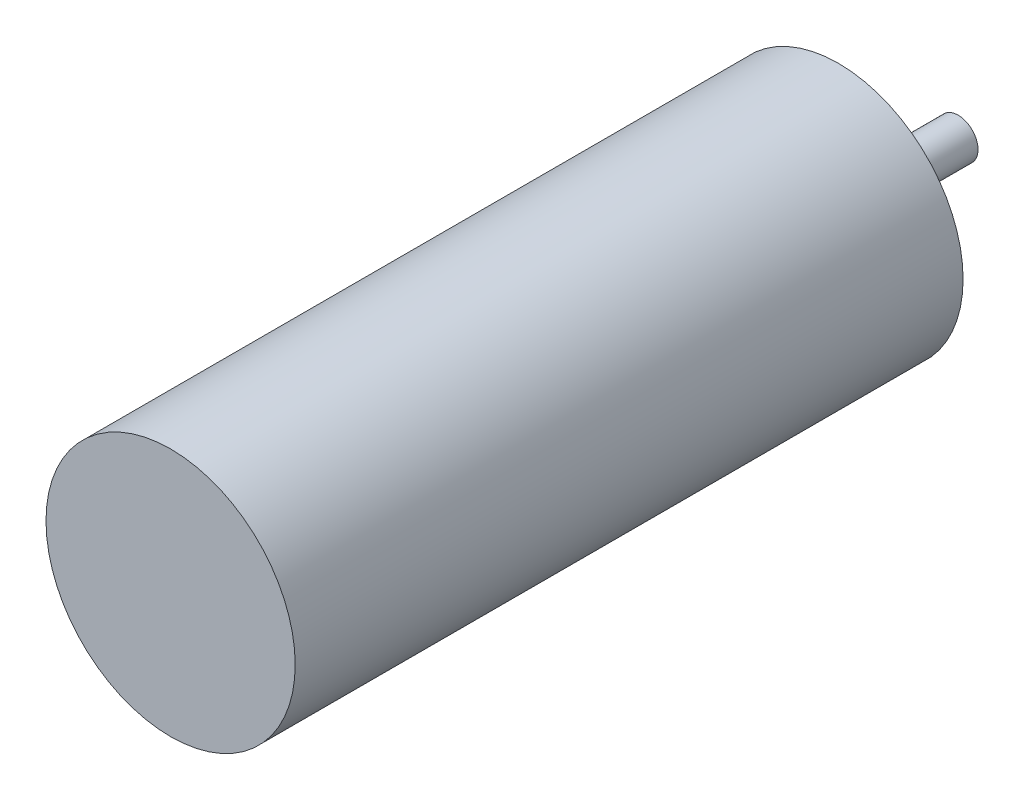
SolidWorks part; units mm, degrees
ref_plane "Front Plane" through (0, 0, 0) normal (0, 0, 1) x (1, 0, 0)
ref_plane "Top Plane" through (0, 0, 0) normal (0, 1, 0) x (1, 0, 0)
ref_plane "Right Plane" through (0, 0, 0) normal (1, 0, 0) x (0, 0, -1)
sketch "Sketch1" plane through (0, 0, 0) normal (0, 0, 1) x (1, 0, 0)
  circle A0 centre (0, 0) radius 12.5
  dimension "D1" = 25
extrude "Boss-Extrude1" add sketch "Sketch1" along normal blind 67
sketch "Sketch2" plane through (0, 0, 0) normal (0, 0, -1) x (-1, 0, 0)
  circle A0 centre (0, 0) radius 4
  dimension "D1" = 8
extrude "Boss-Extrude2" add sketch "Sketch2" along normal blind 3
sketch "Sketch3" plane through (0, 0, -3) normal (0, 0, -1) x (-1, 0, 0)
  circle A0 centre (0, 0) radius 2
  dimension "D1" = 4
extrude "Boss-Extrude3" add sketch "Sketch3" along normal blind 9
